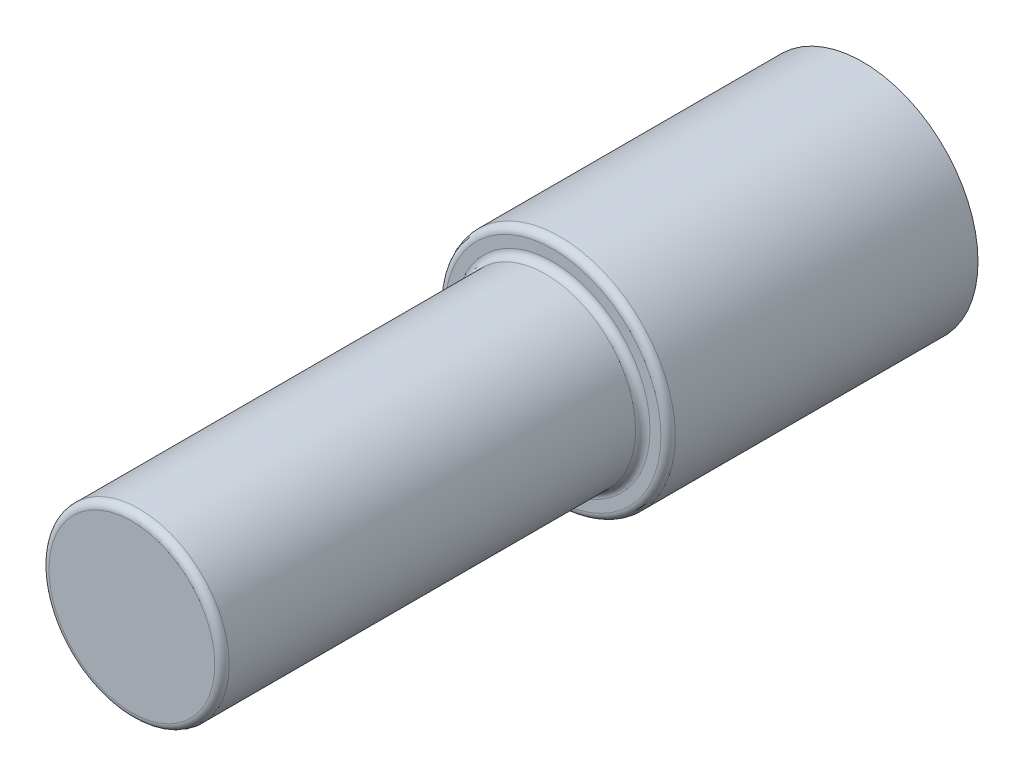
SolidWorks part; units mm, degrees
material "PF"
ref_plane "Front Plane" through (0, 0, 0) normal (0, 0, 1) x (1, 0, 0)
ref_plane "Top Plane" through (0, 0, 0) normal (0, 1, 0) x (1, 0, 0)
ref_plane "Right Plane" through (0, 0, 0) normal (1, 0, 0) x (0, 0, -1)
sketch "Sketch1" plane through (0, 0, 0) normal (0, 0, 1) x (1, 0, 0)
  circle A0 centre (0, 0) radius 16
  dimension "D1" = 32
extrude "Boss-Extrude1" add sketch "Sketch1" along normal blind 43
sketch "Sketch2" plane through (0, 0, 43) normal (0, 0, 1) x (1, 0, 0)
  circle A0 centre (0, 0) radius 12.5
  dimension "D1" = 25
extrude "Boss-Extrude2" add sketch "Sketch2" along normal blind 58.4
sketch "Sketch3" plane through (0, 0, 0) normal (0, 0, -1) x (-1, 0, 0)
  circle A0 centre (0, 0) radius 9.5
  dimension "D1" = 19
extrude "Boss-Extrude3" add sketch "Sketch3" along normal blind 2.25
sketch "Sketch4" plane through (0, 0, -2.25) normal (0, 0, -1) x (-1, 0, 0)
  circle A0 centre (0, 0) radius 5
  dimension "D1" = 10
extrude "Boss-Extrude4" add sketch "Sketch4" along normal blind 2.6
sketch "Sketch5" plane through (0, 0, -4.85) normal (0, 0, -1) x (-1, 0, 0)
  circle A0 centre (0, 0) radius 3
  dimension "D1" = 6
extrude "Cut-Extrude1" cut sketch "Sketch5" against normal blind 5
fillet "Fillet1" radius 1 3 edges at (12.5, 0, 43) (16, 0, 43) (12.5, 0, 101.4)
hole_wizard "M3x0.5 Tapped Hole1" positions "Sketch8" profile "Sketch7" tap size "M3x0.5" standard "Ansi Metric"
sketch "Sketch8" plane through (0, 0, 0) normal (0, 0, -1) x (-1, 0, 0)
  circle A0 centre (0, 0) radius 13 construction
  point P0 (0, 13)
  point P1 (-13, 0)
  point P3 (0, -13)
  point P5 (13, 0)
  dimension "D1" = 26
sketch "Sketch7" plane through (0, 13, 0) normal (1, 0, 0) x (0, 1, 0)
  line L0 (0, 0) -> (0, 7.0511)
  line L1 (0, 7.0511) -> (1.25, 6.3)
  line L2 (1.25, 6.3) -> (1.25, 0)
  line L5 (1.25, 0) -> (0, 0)
  line L10 (0, 7.0511) -> (-1.25, 6.3) construction
  line L11 (0, -6.35) -> (0, 107.95) construction
  dimension "Tap Drill Dia." = 2.5
  dimension "Tap Drill Depth" = 6.3
  dimension "Drill Angle" = 118
cosmetic thread "Hole Thread1" parameters "D1"=3.8, "D2"=3
cosmetic thread "Hole Thread2" parameters "D1"=3.8, "D2"=3
cosmetic thread "Hole Thread3" parameters "D1"=3.8, "D2"=3
cosmetic thread "Hole Thread4" parameters "D1"=3.8, "D2"=3
